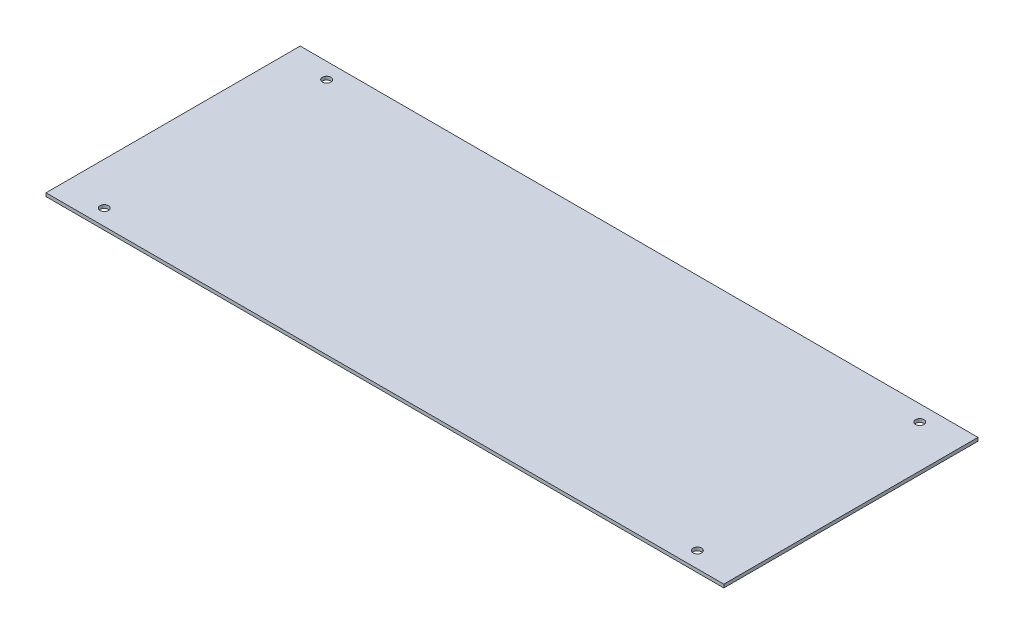
SolidWorks part; units mm, degrees
ref_plane "Front Plane" through (0, 0, 0) normal (0, 0, 1) x (1, 0, 0)
ref_plane "Top Plane" through (0, 0, 0) normal (0, 1, 0) x (1, 0, 0)
ref_plane "Right Plane" through (0, 0, 0) normal (1, 0, 0) x (0, 0, -1)
sketch "Sketch1" plane through (0, 0, 0) normal (0, 1, 0) x (1, 0, 0)
  line L0 (-44.45, 16.6688) -> (44.45, 16.6687) construction
  line L1 (-50.8, 19.05) -> (50.8, 19.05)
  line L2 (-50.8, 19.05) -> (-50.8, -19.05)
  line L3 (-50.8, -19.05) -> (50.8, -19.05)
  line L4 (50.8, 19.05) -> (50.8, -19.05)
  line L5 (-50.8, 19.05) -> (50.8, -19.05) construction
  line L6 (-50.8, -19.05) -> (50.8, 19.05) construction
  line L7 (44.45, 16.6687) -> (44.45, -16.6687) construction
  line L8 (44.45, -16.6687) -> (-44.45, -16.6687) construction
  line L9 (-44.45, -16.6687) -> (-44.45, 16.6688) construction
  circle A0 centre (44.45, 16.6687) radius 0.635
  circle A1 centre (44.45, -16.6687) radius 0.635
  circle A2 centre (-44.45, 16.6688) radius 0.635
  circle A3 centre (-44.45, -16.6687) radius 0.635
  point P0 (0, 0)
  dimension "D3" = 1.27
  dimension "D1" = 38.1
  dimension "D2" = 101.6
  dimension "D4" = 88.9
extrude "Boss-Extrude1" add sketch "Sketch1" along normal blind 0.5
